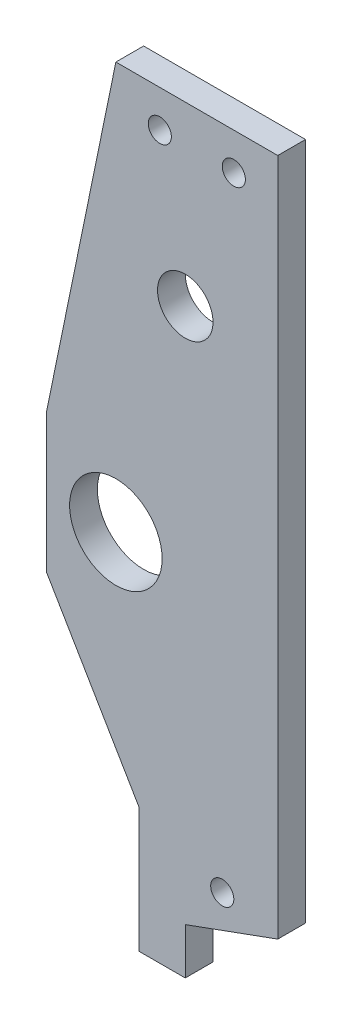
SolidWorks part; units mm, degrees
ref_plane "Front Plane" through (0, 0, 0) normal (0, 0, 1) x (1, 0, 0)
ref_plane "Top Plane" through (0, 0, 0) normal (0, 1, 0) x (1, 0, 0)
ref_plane "Right Plane" through (0, 0, 0) normal (1, 0, 0) x (0, 0, -1)
sketch "Sketch2" plane through (0, 0, 0) normal (0, 0, 1) x (1, 0, 0)
  line L1 (-56.0248, -27.1803) -> (-36.0248, -27.1803)
  line L2 (-56.0248, -27.1803) -> (-56.0248, 49.8197)
  line L3 (-56.0248, 49.8197) -> (-36.0248, 49.8197)
  line L4 (-36.0248, -27.1803) -> (-36.0248, 49.8197)
  dimension "D1" = 77
  dimension "D2" = 20
extrude "Boss-Extrude1" add sketch "Sketch2" along normal blind 3
sketch "Sketch3" plane through (0, 0, 3) normal (0, 0, 1) x (1, 0, 0)
  line L0 (-56.0248, 49.8197) -> (-56.0248, -27.1803) construction
  line L1 (-56.0248, -1.6803) -> (-71.0248, -1.6803)
  line L2 (-56.0248, -1.6803) -> (-56.0248, 13.3197)
  line L3 (-56.0248, 13.3197) -> (-71.0248, 13.3197)
  line L4 (-71.0248, -1.6803) -> (-71.0248, 13.3197)
  dimension "D1" = 25.5
  dimension "D2" = 15
  dimension "D3" = 15
extrude "Boss-Extrude2" add sketch "Sketch3" against normal blind 3
sketch "Sketch4" plane through (0, 0, 3) normal (0, 0, 1) x (1, 0, 0)
  line L3 (-71.0248, 13.3197) -> (-63.5248, 49.8197)
  line L4 (-63.5248, 49.8197) -> (-56.0248, 49.8197)
  line L5 (-56.0248, 49.8197) -> (-56.0248, 13.3197)
  line L6 (-56.0248, 13.3197) -> (-71.0248, 13.3197)
  line L7 (-71.0248, -1.6803) -> (-56.0248, -27.1803)
  line L8 (-56.0248, -27.1803) -> (-56.0248, -1.6803)
  line L9 (-56.0248, -1.6803) -> (-71.0248, -1.6803)
extrude "Boss-Extrude3" add sketch "Sketch4" against normal blind 3
sketch "Sketch5" plane through (0, 0, 3) normal (0, 0, 1) x (1, 0, 0)
  line L0 (-56.0248, -27.1803) -> (-56.0248, -32.1803)
  line L1 (-56.0248, -32.1803) -> (-61.0248, -32.1803)
  line L2 (-61.0248, -32.1803) -> (-61.0248, -18.6803)
  line L3 (-71.0248, -1.6803) -> (-56.0248, -27.1803) construction
  line L4 (-61.0248, -18.6803) -> (-56.0248, -27.1803)
extrude "Boss-Extrude4" add sketch "Sketch5" against normal blind 3
sketch "Sketch6" plane through (0, 0, 3) normal (0, 0, 1) x (1, 0, 0)
  line L0 (-71.0248, 13.3197) -> (-71.0248, -1.6803) construction
  line L1 (-56.0248, -32.1803) -> (-56.0248, -27.1803) construction
  line L2 (-56.0248, -27.1803) -> (-36.0248, -27.1803) construction
  line L3 (-56.0248, -27.1803) -> (-46.0248, -23.5406)
  line L4 (-36.0248, 49.8197) -> (-46.0248, 49.8197)
  line L5 (-36.0248, 49.8197) -> (-36.0248, -27.1803)
  line L6 (-36.0248, -27.1803) -> (-46.0248, -27.1803)
  line L7 (-46.0248, 49.8197) -> (-46.0248, -23.5406)
  line L8 (-46.0248, -27.1803) -> (-56.0248, -27.1803)
  circle A0 centre (-63.5248, 5.8197) radius 5
  circle A1 centre (-56.0248, 30.7145) radius 3
  circle A2 centre (-52.0248, -22.1803) radius 1.25
  dimension "D1" = 7.5
  dimension "D3" = 26
  dimension "D5" = 5
  dimension "D2" = 7.5
  dimension "D4" = 0
  dimension "D6" = 4
  dimension "D7" = 10
extrude "Cut-Extrude1" cut sketch "Sketch6" against normal through all
sketch "Sketch7" plane through (0, 0, 3) normal (0, 0, 1) x (1, 0, 0)
  line L0 (-46.0248, 49.8197) -> (-63.5248, 49.8197) construction
  circle A0 centre (-58.7748, 45.8197) radius 1.25
  circle A1 centre (-50.7748, 45.8197) radius 1.25
  point P6 (-54.7748, 49.8197)
  point P7 (-54.7748, 49.8197)
  dimension "D1" = 4
  dimension "D2" = 4
  dimension "D3" = 4
  dimension "D4" = 4
extrude "Cut-Extrude2" cut sketch "Sketch7" against normal blind 10
